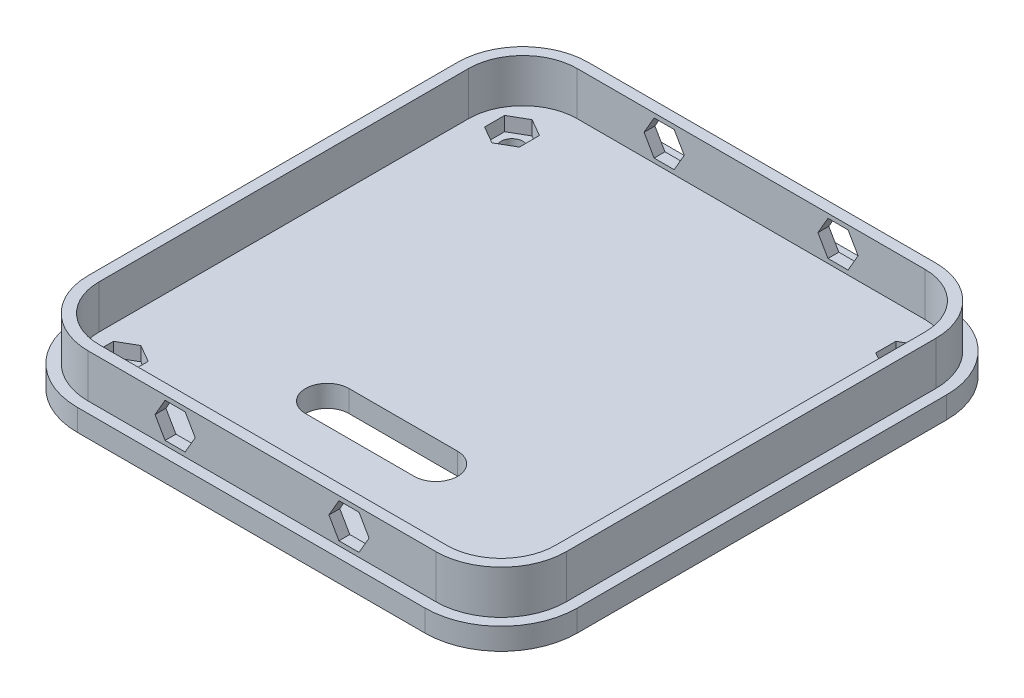
SolidWorks part; units mm, degrees
ref_plane "Front Plane" through (0, 0, 0) normal (0, 0, 1) x (1, 0, 0)
ref_plane "Top Plane" through (0, 0, 0) normal (0, 1, 0) x (1, 0, 0)
ref_plane "Right Plane" through (0, 0, 0) normal (1, 0, 0) x (0, 0, -1)
sketch "Sketch1" plane through (0, 0, 0) normal (0, 1, 0) x (1, 0, 0)
  line L1 (0, 0) -> (220, 0)
  line L2 (0, 0) -> (0, 230)
  line L3 (0, 230) -> (220, 230)
  line L4 (220, 0) -> (220, 230)
  dimension "D1" = 230
  dimension "D2" = 220
extrude "Boss-Extrude1" add sketch "Sketch1" along normal blind 20
sketch "Sketch3" plane through (0, 20, 0) normal (0, 1, 0) x (1, 0, 0)
  line L0 (110, 230) -> (110, 0) construction
  line L1 (0, 230) -> (10, 230)
  line L2 (0, 230) -> (0, 215)
  line L3 (0, 215) -> (10, 215)
  line L4 (10, 230) -> (10, 215)
  line L5 (220, 230) -> (0, 230) construction
  line L6 (0, 0) -> (220, 0) construction
  line L7 (0, 115) -> (220, 115) construction
  line L8 (0, 230) -> (0, 0) construction
  line L9 (220, 0) -> (220, 230) construction
  line L10 (0, 215) -> (0, 200)
  line L11 (0, 215) -> (10, 215)
  line L12 (10, 215) -> (10, 200)
  line L13 (0, 200) -> (10, 200)
  line L14 (0, 200) -> (0, 185)
  line L15 (0, 200) -> (10, 200)
  line L16 (10, 200) -> (10, 185)
  line L17 (0, 185) -> (10, 185)
  line L18 (0, 185) -> (0, 170)
  line L19 (0, 185) -> (10, 185)
  line L20 (10, 185) -> (10, 170)
  line L21 (0, 170) -> (10, 170)
  line L22 (0, 170) -> (0, 155)
  line L23 (0, 170) -> (10, 170)
  line L24 (10, 170) -> (10, 155)
  line L25 (0, 155) -> (10, 155)
  line L26 (0, 155) -> (0, 140)
  line L27 (0, 155) -> (10, 155)
  line L28 (10, 155) -> (10, 140)
  line L29 (0, 140) -> (10, 140)
  line L30 (0, 140) -> (0, 125)
  line L31 (0, 140) -> (10, 140)
  line L32 (10, 140) -> (10, 125)
  line L33 (0, 125) -> (10, 125)
  line L34 (0, 125) -> (0, 110)
  line L35 (0, 125) -> (10, 125)
  line L36 (10, 125) -> (10, 110)
  line L37 (0, 110) -> (10, 110)
  line L38 (0, 110) -> (0, 95)
  line L39 (0, 110) -> (10, 110)
  line L40 (10, 110) -> (10, 95)
  line L41 (0, 95) -> (10, 95)
  line L42 (0, 95) -> (0, 80)
  line L43 (0, 95) -> (10, 95)
  line L44 (10, 95) -> (10, 80)
  line L45 (0, 80) -> (10, 80)
  line L46 (0, 80) -> (0, 65)
  line L47 (0, 80) -> (10, 80)
  line L48 (10, 80) -> (10, 65)
  line L49 (0, 65) -> (10, 65)
  line L50 (0, 65) -> (0, 50)
  line L51 (0, 65) -> (10, 65)
  line L52 (10, 65) -> (10, 50)
  line L53 (0, 50) -> (10, 50)
  line L54 (0, 50) -> (0, 35)
  line L55 (0, 50) -> (10, 50)
  line L56 (10, 50) -> (10, 35)
  line L57 (0, 35) -> (10, 35)
  line L58 (0, 35) -> (0, 20)
  line L59 (0, 35) -> (10, 35)
  line L60 (10, 35) -> (10, 20)
  line L61 (0, 20) -> (10, 20)
  line L62 (0, 20) -> (0, 5)
  line L63 (0, 20) -> (10, 20)
  line L64 (10, 20) -> (10, 5)
  line L65 (0, 5) -> (10, 5)
  line L66 (220, 5) -> (210, 5)
  line L67 (210, 20) -> (210, 5)
  line L68 (220, 20) -> (210, 20)
  line L69 (220, 20) -> (220, 5)
  line L70 (220, 20) -> (210, 20)
  line L71 (210, 35) -> (210, 20)
  line L72 (220, 35) -> (210, 35)
  line L73 (220, 35) -> (220, 20)
  line L74 (220, 35) -> (210, 35)
  line L75 (210, 50) -> (210, 35)
  line L76 (220, 50) -> (210, 50)
  line L77 (220, 50) -> (220, 35)
  line L78 (220, 50) -> (210, 50)
  line L79 (210, 65) -> (210, 50)
  line L80 (220, 65) -> (210, 65)
  line L81 (220, 65) -> (220, 50)
  line L82 (220, 65) -> (210, 65)
  line L83 (210, 80) -> (210, 65)
  line L84 (220, 80) -> (210, 80)
  line L85 (220, 80) -> (220, 65)
  line L86 (220, 80) -> (210, 80)
  line L87 (210, 95) -> (210, 80)
  line L88 (220, 95) -> (210, 95)
  line L89 (220, 95) -> (220, 80)
  line L90 (220, 95) -> (210, 95)
  line L91 (210, 110) -> (210, 95)
  line L92 (220, 110) -> (210, 110)
  line L93 (220, 110) -> (220, 95)
  line L94 (220, 110) -> (210, 110)
  line L95 (210, 125) -> (210, 110)
  line L96 (220, 125) -> (210, 125)
  line L97 (220, 125) -> (220, 110)
  line L98 (220, 125) -> (210, 125)
  line L99 (210, 140) -> (210, 125)
  line L100 (220, 140) -> (210, 140)
  line L101 (220, 140) -> (220, 125)
  line L102 (220, 140) -> (210, 140)
  line L103 (210, 155) -> (210, 140)
  line L104 (220, 155) -> (210, 155)
  line L105 (220, 155) -> (220, 140)
  line L106 (220, 155) -> (210, 155)
  line L107 (210, 170) -> (210, 155)
  line L108 (220, 170) -> (210, 170)
  line L109 (220, 170) -> (220, 155)
  line L110 (220, 170) -> (210, 170)
  line L111 (210, 185) -> (210, 170)
  line L112 (220, 185) -> (210, 185)
  line L113 (220, 185) -> (220, 170)
  line L114 (220, 185) -> (210, 185)
  line L115 (210, 200) -> (210, 185)
  line L116 (220, 200) -> (210, 200)
  line L117 (220, 200) -> (220, 185)
  line L118 (220, 200) -> (210, 200)
  line L119 (210, 215) -> (210, 200)
  line L120 (220, 215) -> (210, 215)
  line L121 (220, 215) -> (220, 200)
  line L122 (210, 230) -> (210, 215)
  line L123 (220, 215) -> (210, 215)
  line L124 (220, 230) -> (220, 215)
  line L125 (220, 230) -> (210, 230)
  line M6 (0, 230) -> (0, 0)
  line M8 (220, 0) -> (220, 230)
  dimension "D1" = 15
  dimension "D2" = 10
  dimension "D3" = 15
fillet "Fillet1" radius 30 4 edges at (0, 10, 0) (220, 10, 0) (220, 10, -230) (0, 10, -230)
extrude "Cut-Extrude2" [suppressed] cut sketch "Sketch3" against normal through all contours L61 L60 L57 M6 | L29 L28 L25 M6 | L21 L20 L17 M6 | L72 L71 L68 M8 | L80 L79 L76 M8 | L88 L87 L84 M8 | L96 L95 L92 M8 | L104 L103 L100 M8 | L112 L111 L108 M8 | L13 L12 L3 M6 | L120 L119 L116 M8 | L50 L53 L52 L51 | L45 L44 L43 L42 | L37 L36 L35 L34
sketch "Sketch4" plane through (0, 0, 0) normal (0, -1, 0) x (-1, 0, 0)
  line L4 (-225, 200) -> (-225, 30)
  line L5 (-225, 200) -> (-225, 30)
  line L6 (5, 30) -> (5, 200)
  line L7 (5, 30) -> (5, 200)
  line L235 (-190, -5) -> (-30, -5)
  line L242 (-30, 235) -> (-190, 235)
  line L249 (-190, -5) -> (-30, -5)
  line L256 (-30, 235) -> (-190, 235)
  arc A32 (-225, 30) -> (-190, -5) centre (-190, 30) ccw
  arc A34 (-30, -5) -> (5, 30) centre (-30, 30) ccw
  arc A36 (5, 200) -> (-30, 235) centre (-30, 200) ccw
  arc A38 (-190, 235) -> (-225, 200) centre (-190, 200) ccw
  arc A40 (-225, 30) -> (-190, -5) centre (-190, 30) ccw
  arc A42 (-30, -5) -> (5, 30) centre (-30, 30) ccw
  arc A44 (5, 200) -> (-30, 235) centre (-30, 200) ccw
  arc A46 (-190, 235) -> (-225, 200) centre (-190, 200) ccw
  dimension "D1" = 5
extrude "Boss-Extrude4" add sketch "Sketch4" along normal blind 10
sketch "Sketch15" plane through (0, 20, 0) normal (0, 1, 0) x (1, 0, 0)
  line L115 (215, 30) -> (215, 200)
  line L118 (190, 225) -> (30, 225)
  line L121 (5, 200) -> (5, 30)
  line L145 (30, 5) -> (190, 5)
  line L169 (215, 30) -> (215, 200)
  line L172 (190, 225) -> (30, 225)
  line L175 (5, 200) -> (5, 30)
  line L199 (30, 5) -> (190, 5)
  arc A8 (215, 200) -> (190, 225) centre (190, 200) ccw
  arc A9 (30, 225) -> (5, 200) centre (30, 200) ccw
  arc A10 (5, 30) -> (30, 5) centre (30, 30) ccw
  arc A11 (190, 5) -> (215, 30) centre (190, 30) ccw
  arc A12 (215, 200) -> (190, 225) centre (190, 200) ccw
  arc A13 (30, 225) -> (5, 200) centre (30, 200) ccw
  arc A14 (5, 30) -> (30, 5) centre (30, 30) ccw
  arc A15 (190, 5) -> (215, 30) centre (190, 30) ccw
  dimension "D1" = 5
extrude "Cut-Extrude10" cut sketch "Sketch15" against normal blind 20
sketch "Sketch6" plane through (0, -10, 0) normal (0, -1, 0) x (-1, 0, 0)
  line L0 (-110, -5) -> (-110, 235) construction
  line L1 (-190, -5) -> (-30, -5) construction
  line L2 (-30, 235) -> (-190, 235) construction
  line L3 (-110, 115) -> (5, 115) construction
  line L4 (-110, 115) -> (-225, 115) construction
  line L5 (-20, -5) -> (-20, 235)
  line L6 (-200, -5) -> (-200, 235)
  line L7 (-110, 25) -> (-225, 25)
  line L8 (-110, 25) -> (5, 25)
  line L9 (-110, 205) -> (-225, 205)
  line L10 (-110, 205) -> (5, 205)
  line L12 (-110, 115) -> (5, 115) construction
  line L13 (5, 30) -> (5, 200) construction
  line L14 (-110, 115) -> (-225, 115) construction
  line L15 (-225, 200) -> (-225, 30) construction
  circle A0 centre (-200, 205) radius 5.025
  circle A1 centre (-20, 205) radius 5.025
  circle A2 centre (-20, 25) radius 5.025
  circle A3 centre (-200, 25) radius 5.025
  point P29 (0, 0)
  point P30 (5, 115)
  point P32 (0, 0)
  point P35 (-225, 115)
  dimension "D5" = 10.05
  dimension "D1" = 90
  dimension "D2" = 90
  dimension "D3" = 90
  dimension "D4" = 90
extrude "Cut-Extrude3" cut sketch "Sketch6" against normal through all contours A3 | A0 | A1 | A2
sketch "Sketch7" plane through (0, 0, 0) normal (0, 0, 1) x (1, 0, 0)
  line L0 (110, 20) -> (110, 0) construction
  line L1 (30, 20) -> (190, 20) construction
  line L2 (30, 0) -> (190, 0) construction
  line L3 (30, 10) -> (190, 10) construction
  line L4 (30, 20) -> (30, 0) construction
  line L5 (190, 0) -> (190, 20) construction
  circle A0 centre (70, 10) radius 5
  circle A1 centre (150, 10) radius 5
  point P14 (110, 10)
  dimension "D2" = 10
  dimension "D1" = 40
sketch "Sketch8" plane through (0, 0, -230) normal (0, 0, -1) x (-1, 0, 0)
  circle A0 centre (-150, 10) radius 5
  circle A1 centre (-70, 10) radius 5
extrude "Cut-Extrude4" cut sketch "Sketch8" against normal blind 30
extrude "Cut-Extrude5" cut sketch "Sketch7" against normal blind 30
sketch "Sketch9" plane through (0, 0, 0) normal (0, 0, 1) x (1, 0, 0)
  line L0 (110, 20) -> (110, 0) construction
  line L1 (60.7624, 10) -> (65.3812, 2)
  line L2 (65.3812, 2) -> (74.6188, 2)
  line L3 (74.6188, 2) -> (79.2376, 10)
  line L4 (79.2376, 10) -> (74.6188, 18)
  line L5 (74.6188, 18) -> (65.3812, 18)
  line L6 (65.3812, 18) -> (60.7624, 10)
  line L7 (30, 20) -> (190, 20) construction
  line L8 (30, 0) -> (190, 0) construction
  line L9 (154.6188, 2) -> (145.3812, 2)
  line L10 (154.6188, 18) -> (159.2376, 10)
  line L11 (145.3812, 18) -> (154.6188, 18)
  line L12 (140.7624, 10) -> (145.3812, 18)
  line L13 (145.3812, 2) -> (140.7624, 10)
  line L14 (159.2376, 10) -> (154.6188, 2)
  circle A0 centre (70, 10) radius 8 construction
  circle A2 centre (150, 10) radius 8 construction
  point P15 (150, 10)
  dimension "D1" = 16
sketch "Sketch10" plane through (0, 0, -230) normal (0, 0, -1) x (-1, 0, 0)
  line L1 (-159.2376, 10) -> (-154.6188, 2)
  line L2 (-154.6188, 2) -> (-145.3812, 2)
  line L3 (-145.3812, 2) -> (-140.7624, 10)
  line L4 (-140.7624, 10) -> (-145.3812, 18)
  line L5 (-145.3812, 18) -> (-154.6188, 18)
  line L6 (-154.6188, 18) -> (-159.2376, 10)
  line L7 (-79.2376, 10) -> (-74.6188, 2)
  line L8 (-74.6188, 2) -> (-65.3812, 2)
  line L9 (-65.3812, 2) -> (-60.7624, 10)
  line L10 (-60.7624, 10) -> (-65.3812, 18)
  line L11 (-65.3812, 18) -> (-74.6188, 18)
  line L12 (-74.6188, 18) -> (-79.2376, 10)
  circle A0 centre (-150, 10) radius 8 construction
  circle A1 centre (-70, 10) radius 8 construction
extrude "Cut-Extrude6" cut sketch "Sketch10" against normal blind 8.5
extrude "Cut-Extrude7" cut sketch "Sketch9" against normal blind 8.5
sketch "Sketch11" plane through (0, 20, 0) normal (0, 1, 0) x (1, 0, 0)
  line L0 (110, 230) -> (110, 0) construction
  line L1 (20, 214.2376) -> (12, 209.6188)
  line L2 (12, 209.6188) -> (12, 200.3812)
  line L3 (12, 200.3812) -> (20, 195.7624)
  line L4 (20, 195.7624) -> (28, 200.3812)
  line L5 (28, 200.3812) -> (28, 209.6188)
  line L6 (28, 209.6188) -> (20, 214.2376)
  line L7 (190, 230) -> (30, 230) construction
  line L8 (30, 0) -> (190, 0) construction
  line L9 (110, 115) -> (225, 115) construction
  line L10 (225, 115) -> (-5, 115) construction
  line L11 (192, 209.6188) -> (200, 214.2376)
  line L12 (192, 200.3812) -> (192, 209.6188)
  line L13 (200, 195.7624) -> (192, 200.3812)
  line L14 (208, 200.3812) -> (200, 195.7624)
  line L15 (208, 209.6188) -> (208, 200.3812)
  line L16 (200, 214.2376) -> (208, 209.6188)
  line L17 (192, 29.6188) -> (192, 20.3812)
  line L18 (200, 34.2376) -> (192, 29.6188)
  line L19 (208, 29.6188) -> (200, 34.2376)
  line L20 (208, 20.3812) -> (208, 29.6188)
  line L21 (200, 15.7624) -> (208, 20.3812)
  line L22 (192, 20.3812) -> (200, 15.7624)
  line L23 (28, 20.3812) -> (20, 15.7624)
  line L24 (28, 29.6188) -> (28, 20.3812)
  line L25 (20, 34.2376) -> (28, 29.6188)
  line L26 (12, 29.6188) -> (20, 34.2376)
  line L27 (12, 20.3812) -> (12, 29.6188)
  line L28 (20, 15.7624) -> (12, 20.3812)
  line L29 (225, 200) -> (225, 30) construction
  line L30 (-5, 30) -> (-5, 200) construction
  circle A0 centre (20, 205) radius 8 construction
  circle A1 centre (200, 205) radius 8 construction
  circle A2 centre (200, 25) radius 8 construction
  circle A3 centre (20, 25) radius 8 construction
  point P18 (200, 205)
  point P28 (200, 25)
  point P37 (20, 25)
  point P46 (225, 115)
  point P49 (-5, 115)
  dimension "D1" = 16
extrude "Cut-Extrude8" cut sketch "Sketch11" against normal blind 26.5
sketch "Sketch13" plane through (0, -10, 0) normal (0, -1, 0) x (1, 0, 0)
  line L21 (30, -235) -> (190, -235) construction
  line L49 (190, 5) -> (30, 5) construction
  line L168 (110, 5) -> (110, -235) construction
  line L169 (135, -55) -> (85, -55) construction
  line L170 (135, -65) -> (85, -65)
  line L171 (135, -45) -> (85, -45)
  arc A12 (135, -65) -> (135, -45) centre (135, -55) ccw
  arc A13 (85, -45) -> (85, -65) centre (85, -55) ccw
  point P2 (110, -55)
  point P7 (110, -115)
  dimension "D2" = 10
  dimension "D1" = 60
  dimension "D3" = 50
extrude "Cut-Extrude9" cut sketch "Sketch13" against normal through all
